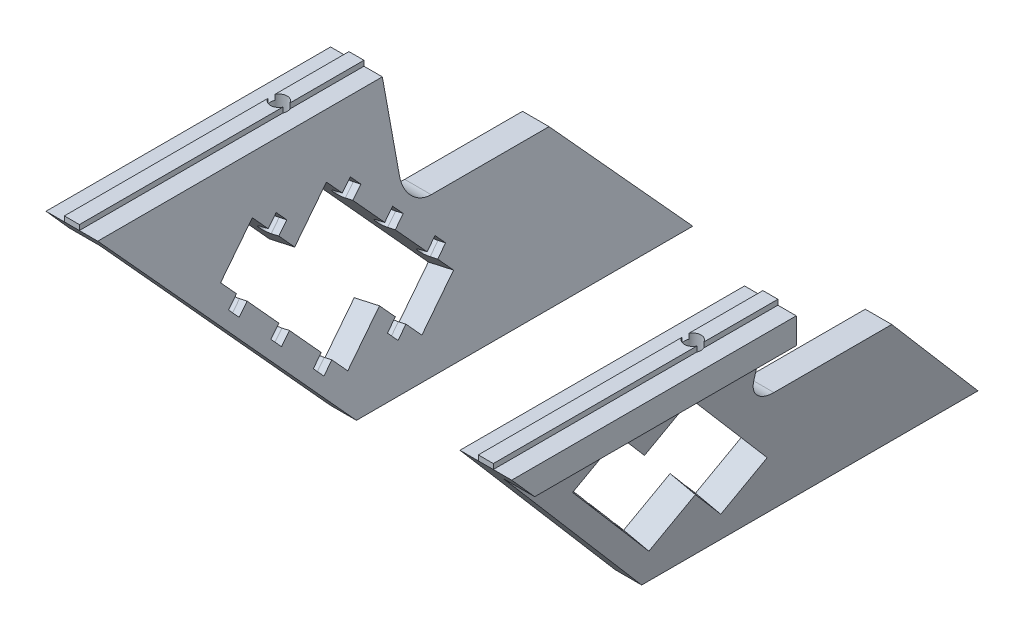
SolidWorks part; units mm, degrees
ref_plane "Front Plane" through (0, 0, 0) normal (0, 0, 1) x (1, 0, 0)
ref_plane "Top Plane" through (0, 0, 0) normal (0, 1, 0) x (1, 0, 0)
ref_plane "Right Plane" through (0, 0, 0) normal (1, 0, 0) x (0, 0, -1)
sketch "Sketch1" plane through (0, 0, 0) normal (0, 0, 1) x (1, 0, 0)
  line L0 (20, 45) -> (20, 40)
  line L1 (20, 40) -> (14.0109, 40)
  line L2 (14.0109, 40) -> (5.122, 0)
  line L3 (5.122, 0) -> (0, 0)
  line L4 (0, 0) -> (10, 45)
  line L5 (10, 45) -> (13.55, 45)
  line L6 (13.55, 45) -> (13.55, 46)
  line L7 (13.55, 46) -> (16.45, 46)
  line L8 (16.45, 46) -> (16.45, 45)
  line L9 (16.45, 45) -> (20, 45)
  line L10 (5.122, 0) -> (34.2968, 0) construction
  dimension "D1" = 10
  dimension "D2" = 2.9
  dimension "D3" = 5
  dimension "D4" = 10
  dimension "D5" = 5
  dimension "D6" = 45
  dimension "D7" = 1
extrude "Main" add sketch "Sketch1" along normal mid plane 105
sketch "Sketch3" plane through (0, 46, 0) normal (0, 1, 0) x (1, 0, 0)
  line L0 (16.45, -52.5) -> (13.55, -52.5) construction
  line L1 (14.0109, -52.5) -> (20, -52.5) construction
  line L2 (20, -52.5) -> (20, 52.5) construction
  circle A0 centre (15, -12.5) radius 1.6
  dimension "D1" = 40
  dimension "D2" = 3.2
  dimension "D4" = 5
extrude "MakerBeamFixHoles" cut sketch "Sketch3" against normal through all
sketch "Sketch2" plane through (0, 40.6155, 0) normal (1, 0, 0) x (0, 0, 1)
  line L0 (-52.5, 40.6155) -> (-12.5, -4.3845)
  line L1 (52.5, -4.3845) -> (-52.5, -4.3845) construction
  line L3 (52.5, 40.6155) -> (-52.5, 40.6155) construction
  line L4 (-12.5, -4.3845) -> (-12.5, -5.3845)
  line L5 (-52.5, 40.6155) -> (-52.5, -5.3845)
  line L6 (52.5, -4.3845) -> (52.5, 40.6155)
  line L7 (52.5, 40.6155) -> (12.5, 40.6155)
  line L8 (12.5, 40.6155) -> (52.5, -4.3845)
  line L9 (52.5, -5.3845) -> (13.1764, -5.3845) construction
  line L10 (-12.5, -5.3845) -> (-52.5, -5.3845)
  dimension "D1" = 40
extrude "SideCut" cut sketch "Sketch2" against normal through all and the other way through all
sketch "Sketch5" plane through (0, 0, 0) normal (-0.9762, 0.2169, 0) x (0, 0, 1)
  line L0 (24.6312, 36.8678) -> (18.0774, 29.3149)
  line L1 (24.6312, 36.8678) -> (32.1842, 30.314)
  line L2 (32.1842, 30.314) -> (12.5226, 7.6551)
  line L3 (12.5226, 7.6551) -> (4.9696, 14.209)
  line L4 (18.0774, 29.3149) -> (10.5244, 35.8687)
  line L5 (12.5, 0) -> (52.5, 46.0977) construction
  line L6 (52.5, 46.8678) -> (13.1764, 46.8678) construction
  line L7 (10.5244, 35.8687) -> (-9.1372, 13.2099)
  line L12 (4.9696, 14.209) -> (-1.5842, 6.656)
  line L13 (-1.5842, 6.656) -> (-9.1372, 13.2099)
  dimension "D1" = 5
  dimension "D2" = 10
  dimension "D3" = 10
  dimension "D4" = 30
  dimension "D6" = 10
  dimension "D7" = 10
  dimension "D8" = 10
extrude "CentralCut" cut sketch "Sketch5" against normal blind 10
ref_plane "Plane1" through (0.0794, 0.3575, -0.4221) normal (0.1422, 0.6398, -0.7553) x (-0.9898, 0.0919, -0.1085)
ref_plane "Plane2" through (1.5012, 6.7553, -7.975) normal (0.1422, 0.6398, -0.7553) x (-0.9898, 0.0919, -0.1085)
sketch "Sketch4" plane through (-0.6314, 4.6587, 9.7074) normal (-0.1422, -0.6398, 0.7553) x (-0.9898, 0.0919, -0.1085)
  line L0 (-2.3156, -3.9669) -> (-7.2814, -33.553) construction
  line L1 (-12.2124, -32.7254) -> (-7.2814, -33.553) construction
  line L2 (-6.2469, -27.3892) -> (-6.6607, -29.8547)
  line L3 (-6.6607, -29.8547) -> (-8.14, -29.6064)
  line L5 (-6.2469, -27.3892) -> (-7.7262, -27.1409)
  arc A1 (-7.7262, -27.1409) -> (-8.14, -29.6064) centre (-7.9331, -28.3737) ccw
  dimension "D1" = 1.5
  dimension "D2" = 1.25
  dimension "D3" = 5
extrude "RollerSupportHoles" cut sketch "Sketch4" along normal blind 2.5
ref_plane "MirrorPlane" through (-25, 0, 0) normal (1, 0, 0) x (0, 0, -1)
pattern_linear "LPattern1" count 3 spacing 10 along (-0.1638, -0.7373, -0.6554) of "RollerSupportHoles"
sketch "Sketch6" plane through (-0.9868, -4.4408, 5.2426) normal (0.1422, 0.6398, -0.7553) x (-0.9898, 0.0919, -0.1085)
  line L0 (-5.0054, 29.8219) -> (-4.5916, 27.3564)
  line L1 (-4.5916, 27.3564) -> (-6.0709, 27.1081)
  line L2 (-5.0054, 29.8219) -> (-6.4847, 29.5736)
  arc A0 (-6.4847, 29.5736) -> (-6.0709, 27.1081) centre (-6.2778, 28.3408) ccw
  arc A1 (-6.4847, 29.5736) -> (-6.0709, 27.1081) centre (-6.2778, 28.3408) ccw construction
extrude "Cut-Extrude1" cut sketch "Sketch6" along normal blind 25
mirror "Mirror5" about plane through (0.0794, 0.3575, -0.4221) normal (0.1422, 0.6398, -0.7553) of "RollerSupportHoles"
sketch "Sketch7" plane through (-0.9868, -4.4408, 5.2426) normal (0.1422, 0.6398, -0.7553) x (-0.9898, 0.0919, -0.1085)
  line L0 (-4.4156, 17.246) -> (-2.9363, 17.4943)
  line L1 (-2.9363, 17.4943) -> (-3.3501, 19.9598)
  line L2 (-3.3501, 19.9598) -> (-4.8294, 19.7115)
  arc A0 (-4.8294, 19.7115) -> (-4.4156, 17.246) centre (-4.6225, 18.4788) ccw
  arc A1 (-4.8294, 19.7115) -> (-4.4156, 17.246) centre (-4.6225, 18.4788) ccw construction
extrude "Cut-Extrude2" cut sketch "Sketch7" along normal blind 25
sketch "Sketch8" plane through (1.5012, 6.7553, -7.975) normal (0.1422, 0.6398, -0.7553) x (-0.9898, 0.0919, -0.1085)
  line L0 (-2.7603, 7.384) -> (-1.281, 7.6322)
  line L1 (-1.281, 7.6322) -> (-1.6948, 10.0978)
  line L2 (-1.6948, 10.0978) -> (-3.1741, 9.8495)
  arc A0 (-3.1741, 9.8495) -> (-2.7603, 7.384) centre (-2.9672, 8.6167) ccw
extrude "Cut-Extrude3" cut sketch "Sketch8" against normal mid plane 15
sketch "Sketch10" plane through (0, 40, 0) normal (0, -1, 0) x (1, 0, 0)
  circle A2 centre (15, 12.5) radius 4.25
  arc A3 (14.0109, 11.2424) -> (14.0109, 13.7576) centre (15, 12.5) ccw construction
extrude "Cut-Extrude5" cut sketch "Sketch10" along normal blind 5
sketch "Sketch11" plane through (-25, -227.7443, 0) normal (1, 0, 0) x (0, 0, 1)
  line L1 (-30.2778, -252.7443) -> (-2.5, -252.7443)
  line L2 (-30.2778, -252.7443) -> (-30.2778, -287.7443)
  line L3 (-30.2778, -287.7443) -> (-2.5, -287.7443)
  line L4 (-2.5, -252.7443) -> (-2.5, -287.7443)
  line L7 (-12.5, -272.7443) -> (-52.5, -227.7443) construction
  line L9 (12.5, -227.7443) -> (-52.5, -227.7443) construction
  dimension "D1" = 25
  dimension "D2" = 35
  dimension "D3" = 55
extrude "Cut-Extrude6" cut sketch "Sketch11" against normal through all both and the other way through all
fillet "Fillet1" radius 5 1 edges at (8.1165, 25, -2.5)
mirror "Mirror7" about plane through (-25, 0, 0) normal (1, 0, 0) of bodies 123
sketch "Sketch12" [suppressed] plane through (0, 0, 0) normal (0, 0, 1) x (1, 0, 0)
  line L1 (-10.9634, 55.9808) -> (29.8801, 55.9808)
  line L2 (-10.9634, 55.9808) -> (-10.9634, -13.6747)
  line L3 (-10.9634, -13.6747) -> (29.8801, -13.6747)
  line L4 (29.8801, 55.9808) -> (29.8801, -13.6747)
extrude "Cut-Extrude7" [suppressed] cut sketch "Sketch12" against normal through all
